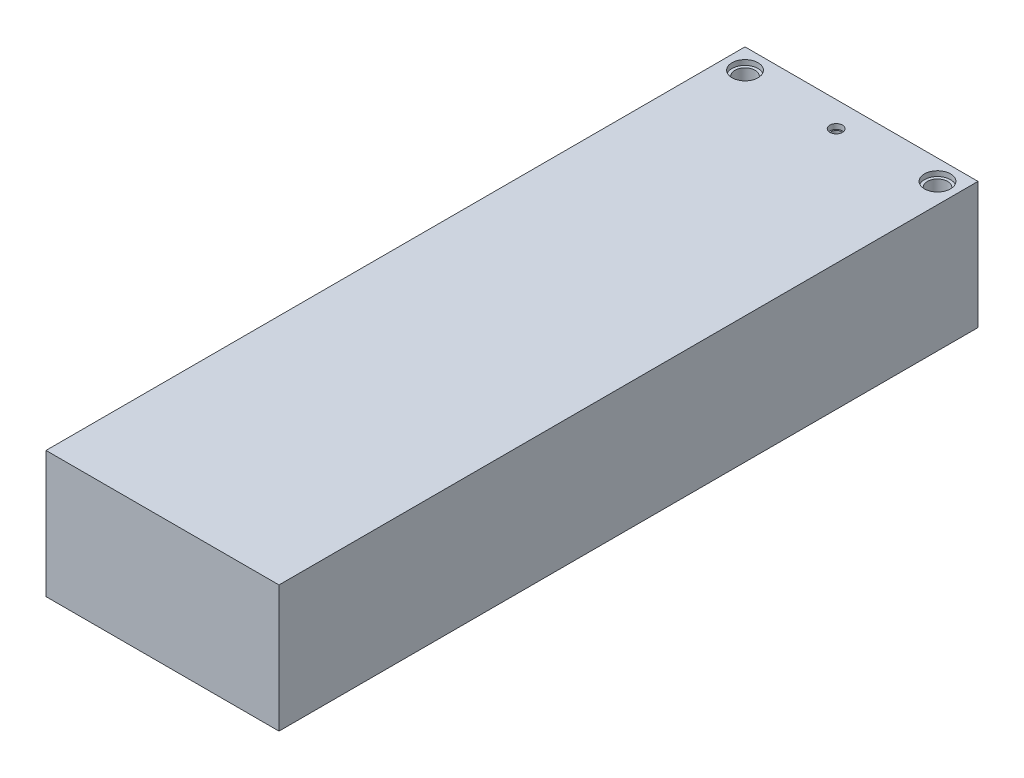
SolidWorks part; units mm, degrees
ref_plane "Front Plane" through (0, 0, 0) normal (0, 0, 1) x (1, 0, 0)
ref_plane "Top Plane" through (0, 0, 0) normal (0, 1, 0) x (1, 0, 0)
ref_plane "Right Plane" through (0, 0, 0) normal (1, 0, 0) x (0, 0, -1)
sketch "Sketch2" plane through (0, 0, 0) normal (0, 0, 1) x (1, 0, 0)
  line L0 (0, 15.7927) -> (0, -15.9075) construction
  line L1 (-23, 12.5) -> (23, 12.5)
  line L2 (-23, 12.5) -> (-23, -12.5)
  line L3 (-23, -12.5) -> (23, -12.5)
  line L4 (23, 12.5) -> (23, -12.5)
  line L5 (26.0243, 0) -> (-25.0811, 0) construction
  point P4 (0, 12.5)
  point P11 (-23, 0)
  dimension "D1" = 25
  dimension "D2" = 46
extrude "Boss-Extrude1" add sketch "Sketch2" along normal blind 138
sketch "Sketch3" plane through (0, 12.5, 0) normal (0, 1, 0) x (1, 0, 0)
  line L0 (-23, -138) -> (-23, 0) construction
  line L1 (23, 0) -> (-23, 0) construction
  line L2 (23, -138) -> (23, 0) construction
  circle A0 centre (-19, -4) radius 2.575
  circle A1 centre (0, -5) radius 1.25
  circle A2 centre (19, -4) radius 2.575
  dimension "D1" = 5.15
  dimension "D2" = 2.5
  dimension "D3" = 4
  dimension "D4" = 4
  dimension "D5" = 5
  dimension "D6" = 4
  dimension "D7" = 4
extrude "Cut-Extrude1" cut sketch "Sketch3" against normal blind 1
sketch "Sketch4" plane through (0, 12.5, 0) normal (0, 1, 0) x (1, 0, 0)
  circle A0 centre (-19, -4) radius 2
  circle A1 centre (19, -4) radius 2
  circle A2 centre (0, -5) radius 1
  dimension "D1" = 4
  dimension "D2" = 2
extrude "Cut-Extrude2" cut sketch "Sketch4" against normal blind 16.5
